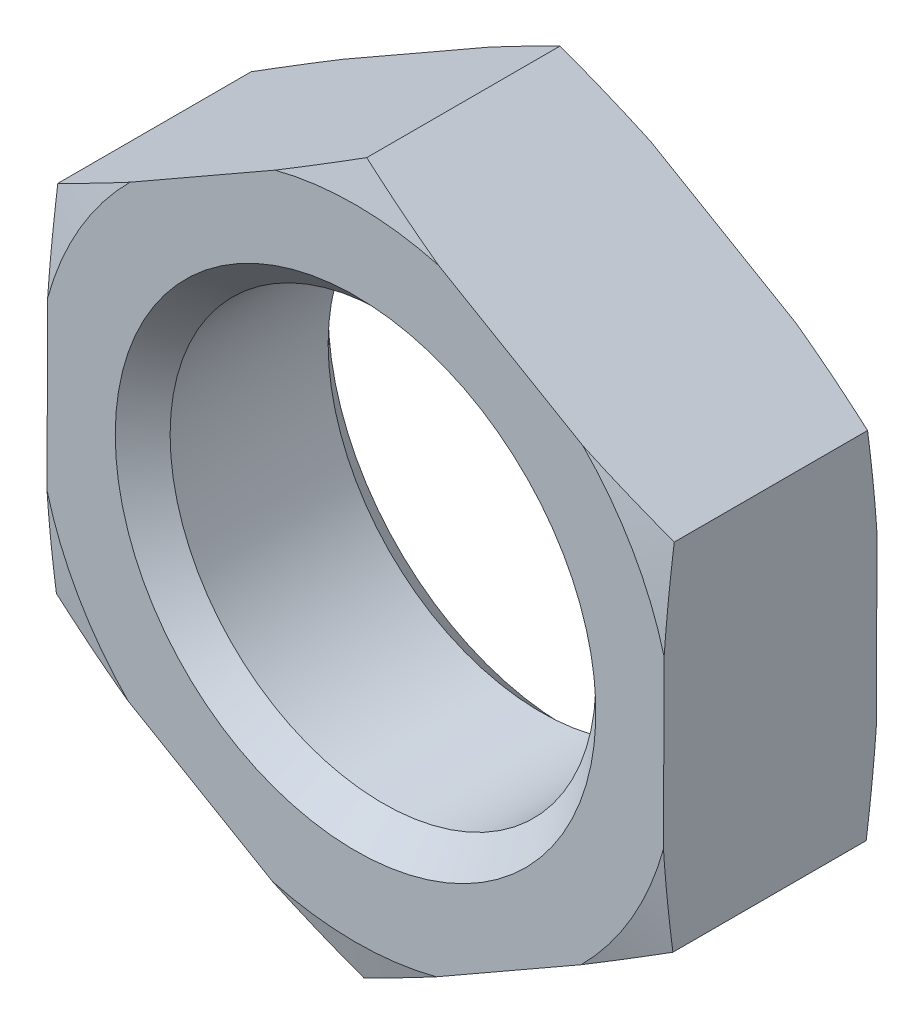
SolidWorks part; units mm, degrees
extrude "基体-拉伸" add sketch "草图1" along normal blind 8
sketch "草图1" plane through (0, 0, 0) normal (0, 0, 1) x (1, 0, 0)
  line L0 (-26.8088, 0) -> (37.1748, 0) construction
  line L1 (0, 25.0215) -> (0, -25.0215) construction
  line L3 (0.0526, 13.3749) -> (-11.5567, 6.733)
  line L4 (-11.5567, 6.733) -> (-11.6093, -6.6419)
  line L5 (-11.6093, -6.6419) -> (-0.0526, -13.3749)
  line L6 (-0.0526, -13.3749) -> (11.5567, -6.733)
  line L7 (11.5567, -6.733) -> (11.6093, 6.6419)
  line L8 (11.6093, 6.6419) -> (0.0526, 13.3749)
  circle A0 centre (0, 0) radius 11.5831 construction
  circle A1 centre (0, 0) radius 8
  dimension "D" = 16
  dimension "e" = 26.75
cosmetic thread "装饰螺纹线1"
chamfer "倒角1" distance 1.031 angle 45 2 edges at (8, 0, 0) (8, 0, 8)
ref_plane "基准面1" through (0, 0, 0) normal (0, 0, 1) x (1, 0, 0)
ref_plane "基准面2" through (0, 0, 0) normal (0, 1, 0) x (1, 0, 0)
ref_plane "基准面3" through (0, 0, 0) normal (1, 0, 0) x (0, 0, -1)
sketch "尺寸草图" plane through (0, 0, 0) normal (0, 0, 1) x (1, 0, 0)
  line L0 (0, 0) -> (24.1005, 0)
  line L1 (0, 0) -> (17.3, 0)
  line L2 (46.8781, 0) -> (69.3781, 0)
  line L3 (-15.2381, 0) -> (0, 0)
  point P3 (16, 0)
  point P4 (2.5, 0)
  point P5 (26.75, 0)
  point P6 (8, 0)
  point P7 (7.3, 0)
  point P8 (24, 0)
  dimension "D" = 16
  dimension "e" = 26.75
  dimension "P" = 2.5
  dimension "m" = 8
  dimension "mw" = 7.3
  dimension "s" = 24
  dimension "da" = 17.3
  dimension "dw" = 22.5
  dimension "D1" = 15.2381
sketch "草图2" plane through (0, 0, 0) normal (0, 0, -1) x (-1, 0, 0)
  circle A0 centre (0, 0) radius 12
  circle A1 centre (0, 0) radius 8 construction
  dimension "s" = 24
extrude "切除-拉伸1" cut sketch "草图2" against normal through all draft 75 flip side to cut
sketch "草图3" plane through (0, 0, 8) normal (0, 0, 1) x (1, 0, 0)
  circle A0 centre (0, 0) radius 12
  dimension "D1" = 24
extrude "切除-拉伸2" cut sketch "草图3" against normal through all draft 75 flip side to cut
equation "\"e@草图1\" = \"e@尺寸草图\""
equation "\"D1@尺寸草图\" = \"D@尺寸草图\" / 1.05"
equation "\"D@草图1\" = \"D@尺寸草图\""
equation "\"m@基体-拉伸\" = \"m@尺寸草图\""
equation "\"D1@草图3\" = \"s@尺寸草图\""
equation "\"s@草图2\" = \"s@尺寸草图\""
equation "\"D2@装饰螺纹线1\" = 1.05 * \"D1@尺寸草图\""
equation "\"D1@倒角1\" =  ( \"da@尺寸草图\" - \"D1@尺寸草图\" )  / 2"
